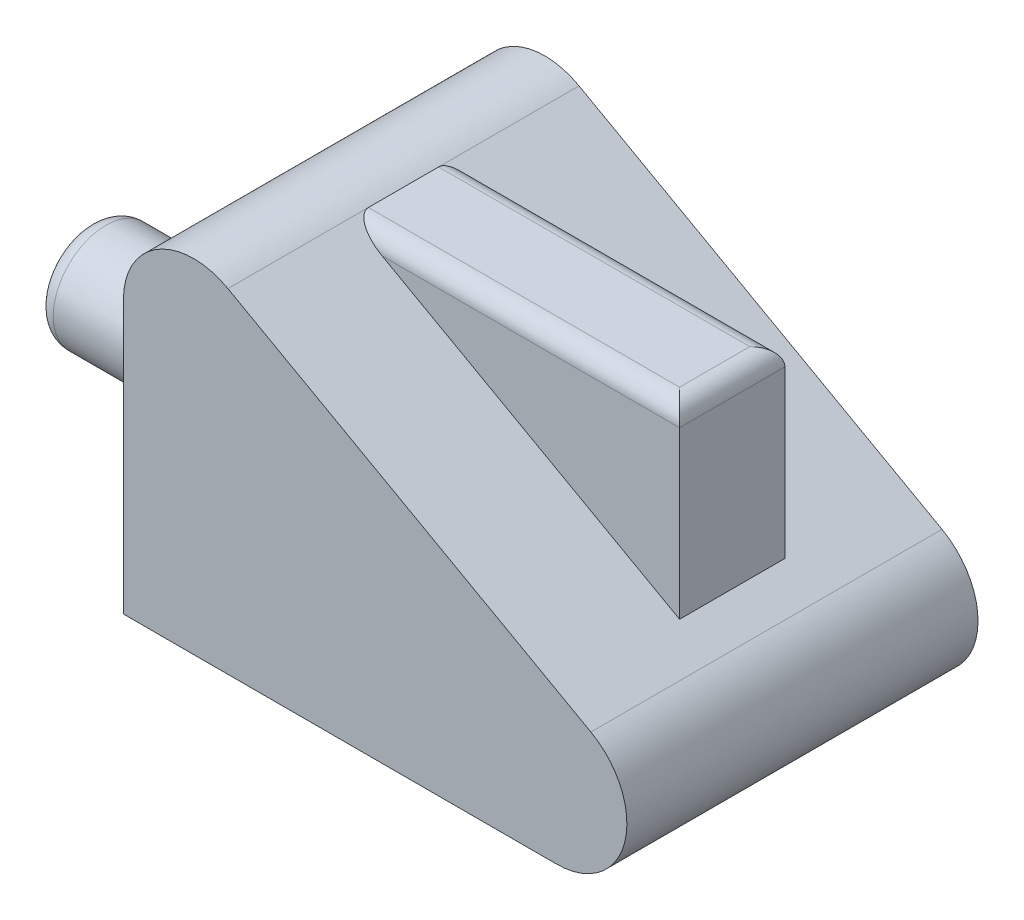
SolidWorks part; units mm, degrees
ref_plane "Front Plane" through (0, 0, 0) normal (0, 0, 1) x (1, 0, 0)
ref_plane "Top Plane" through (0, 0, 0) normal (0, 1, 0) x (1, 0, 0)
ref_plane "Right Plane" through (0, 0, 0) normal (1, 0, 0) x (0, 0, -1)
sketch "Sketch1" plane through (0, 0, 0) normal (0, 0, 1) x (1, 0, 0)
  line L2 (-3, 2.17) -> (-3, 0.67)
  line L5 (-3, 2.17) -> (0, 2.17)
  line L6 (-3, 0.67) -> (0, 0.67)
  line L9 (1.4873, 4.7574) -> (6.6562, 1.8733)
  line L10 (0, 3.8841) -> (0, 0)
  line L12 (-4, 1.42) -> (8.8322, 1.42) construction
  line L14 (0, 0) -> (6.1689, 0)
  arc A0 (6.1689, 0) -> (6.6562, 1.8733) centre (6.1689, 1) ccw
  arc A1 (0, 3.8841) -> (1.4873, 4.7574) centre (1, 3.8841) cw
  dimension "D1" = 1
extrude "Boss-Extrude1" add sketch "Sketch1" along normal blind 5 contours L10 L12 A0 L9 A1 | L12 L2 L6 L10 | L2 L12 L10 L5 | L12 L10 L14 A0
sketch "Sketch2" plane through (-3, 0, 0) normal (-1, 0, 0) x (0, 0, 1)
  line L1 (-1.0751, 2.7436) -> (5.8776, 2.7436)
  line L2 (-1.0751, 2.7436) -> (-1.0751, 0.1921)
  line L3 (-1.0751, 0.1921) -> (5.8776, 0.1921)
  line L4 (5.8776, 2.7436) -> (5.8776, 0.1921)
  circle A0 centre (2.5, 1.42) radius 0.75
extrude "Cut-Extrude1" cut sketch "Sketch2" against normal up to surface (3 mm away) up to face at (0, 3.0271, 2.5)
sketch "Sketch3" plane through (0, 0, 0) normal (0, -1, 0) x (1, 0, 0)
  line L2 (1.4873, 3.25) -> (6.1689, 3.25)
  line L3 (6.1689, 5) -> (6.1689, 0) construction
  line L4 (6.1689, 3.25) -> (6.1689, 1.75)
  line L5 (6.1689, 1.75) -> (1.4873, 1.75)
  line L6 (1.4873, 5) -> (1.4873, 0) construction
  line L7 (1.4873, 3.25) -> (1.4873, 1.75)
extrude "Boss-Extrude2" add sketch "Sketch3" against normal up to vertex (4.7574 mm away)
fillet "Fillet1" radius 0.25 1 edges at (-3, 0.67, 2.5)
fillet "Fillet2" radius 0.25 3 edges at (6.1689, 4.7574, 2.5) (3.8281, 4.7574, 1.75) (3.8281, 4.7574, 3.25)
